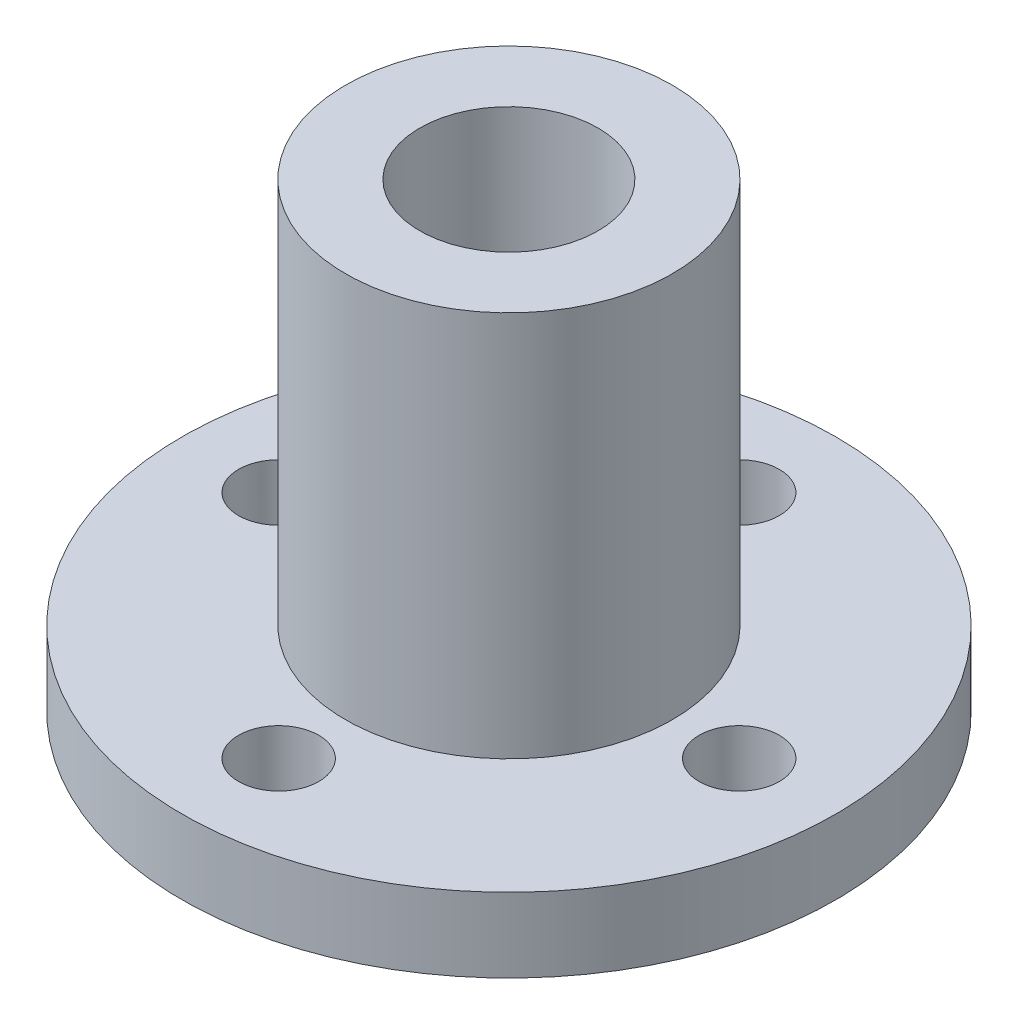
SolidWorks part; units mm, degrees
ref_plane "Front Plane" through (0, 0, 0) normal (0, 0, 1) x (1, 0, 0)
ref_plane "Top Plane" through (0, 0, 0) normal (0, 1, 0) x (1, 0, 0)
ref_plane "Right Plane" through (0, 0, 0) normal (1, 0, 0) x (0, 0, -1)
sketch "Sketch1" plane through (0, 0, 0) normal (0, 0, 1) x (1, 0, 0)
  line L0 (0, 0) -> (0, 54.9474) construction
  line L1 (6, 0) -> (22, 0)
  line L2 (22, 0) -> (22, 5)
  line L3 (22, 5) -> (11, 5)
  line L4 (11, 5) -> (11, 31)
  line L5 (11, 31) -> (6, 31)
  line L6 (6, 31) -> (6, 0)
  dimension "D1" = 12
  dimension "D2" = 22
  dimension "D3" = 44
  dimension "D4" = 31
  dimension "D5" = 5
revolve "Revolve1" add sketch "Sketch1" angle 360 about L0
sketch "Sketch2" plane through (0, 0, 0) normal (0, -1, 0) x (1, 0, 0)
  line L0 (0, 15.5) -> (0, -15.5) construction
  line L1 (-15.5, 0) -> (15.5, 0) construction
  circle A0 centre (0, 15.5) radius 2.7
  circle A1 centre (15.5, 0) radius 2.7
  circle A2 centre (0, -15.5) radius 2.7
  circle A3 centre (-15.5, 0) radius 2.7
  dimension "D2" = 5.4
  dimension "D1" = 31
extrude "Cut-Extrude1" cut sketch "Sketch2" against normal blind 10
